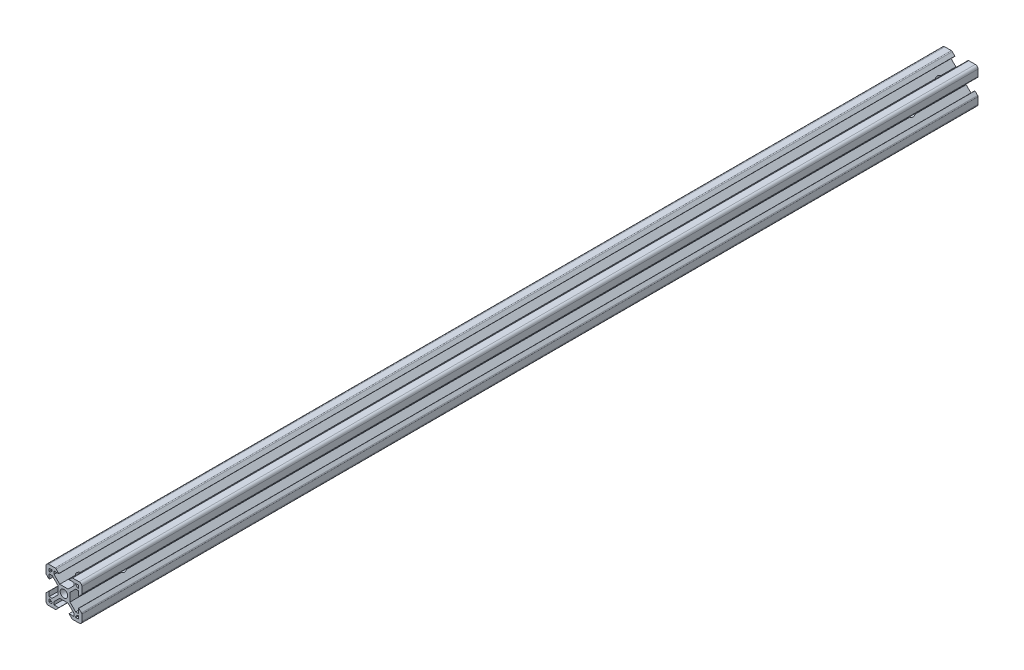
SolidWorks part; units mm, degrees
ref_plane "Front Plane" through (0, 0, 0) normal (0, 0, 1) x (1, 0, 0)
ref_plane "Top Plane" through (0, 0, 0) normal (0, 1, 0) x (1, 0, 0)
ref_plane "Right Plane" through (0, 0, 0) normal (1, 0, 0) x (0, 0, -1)
sketch "Sketch2" plane through (0, 0, 0) normal (0, 0, 1) x (1, 0, 0)
  line L0 (-8.2, 2.89) -> (-8.2, 5.5)
  line L1 (-2.1, 0) -> (-10, 0) construction
  line L2 (0, 2.1) -> (0, 10) construction
  line L3 (-4.9072, 10) -> (-8.5, 10)
  line L4 (-10, 4.9072) -> (-10, 8.5)
  line L5 (-2.1, 0) -> (-3.4, 0) construction
  line L6 (0, 2.1) -> (0, 3.4) construction
  line L7 (0, 3.4) -> (-2.3393, 3.4)
  line L8 (-3.4, 0) -> (-3.4, 2.3393)
  line L9 (-2.89, 8.2) -> (-5.5, 8.2)
  line L10 (-6.57, 8.2) -> (-6.57, 7.66)
  line L11 (-8.2, 6.57) -> (-7.66, 6.57)
  line L12 (-5.5, 8.2) -> (-5.5, 6.5607)
  line L13 (-6.5607, 5.5) -> (-8.2, 5.5)
  line L14 (-8.2, 8.2) -> (-1.4849, 1.4849) construction
  line L15 (-6.5607, 5.5) -> (-3.4, 2.3393)
  line L16 (-5.5, 6.5607) -> (-2.3393, 3.4)
  line L17 (-7.66, 6.57) -> (-6.57, 7.66)
  line L18 (-8.7303, 7.6697) -> (-0.5303, -0.5303) construction
  line L19 (-7.6697, 8.7303) -> (0.5303, 0.5303) construction
  line L20 (-8.2, 8.2) -> (0, 0) construction
  line L21 (-8.2, 6.57) -> (-8.2, 8.2)
  line L22 (-8.2, 0) -> (-8.2, 8.2) construction
  line L23 (-6.57, 8.2) -> (-8.2, 8.2)
  line L24 (0, 8.2) -> (-8.2, 8.2) construction
  line L25 (-10, 0) -> (-10, 10) construction
  line L26 (0, 10) -> (-10, 10) construction
  line L27 (-2.89, 8.31) -> (-2.89, 8.2)
  line L29 (-8.31, 2.89) -> (-8.2, 2.89)
  line L30 (-4.3486, 9.7686) -> (-2.89, 8.31)
  line L31 (-8.31, 2.89) -> (-9.7686, 4.3486)
  arc A0 (0, 2.1) -> (-2.1, 0) centre (0, 0) ccw
  arc A1 (-10, 8.5) -> (-8.5, 10) centre (-8.5, 8.5) cw
  arc A2 (-9.7686, 4.3486) -> (-10, 4.9072) centre (-9.21, 4.9072) cw
  arc A3 (-4.3486, 9.7686) -> (-4.9072, 10) centre (-4.9072, 9.21) ccw
  point P29 (-10, 10)
  point P39 (-10, 4.58)
  point P42 (-4.58, 10)
  dimension "D3" = 2.1
  dimension "D15" = 1.5
  dimension "D22" = 0.79
  dimension "D1" = 10
  dimension "D2" = 10
  dimension "D4" = 1.8
  dimension "D5" = 3.43
  dimension "D6" = 3.43
  dimension "D7" = 0.54
  dimension "D8" = 0.54
  dimension "D9" = 1.07
  dimension "D10" = 1.07
  dimension "D11" = 3.4
  dimension "D12" = 3.4
  dimension "D16" = 7.11
  dimension "D17" = 0.11
  dimension "D18" = 1.69
  dimension "D19" = 0.11
  dimension "D20" = 7.11
  dimension "D21" = 1.69
  dimension "D13" = 0.75
  dimension "D14" = 0.75
sketch "Sketch6" plane through (0, 0, 0) normal (0, 0, 1) x (1, 0, 0)
  line L0 (-3.4, 0) -> (-3.4, 2.3393) construction
  line L1 (-6.5607, 5.5) -> (-3.4, 2.3393) construction
  line L2 (-6.5607, 5.5) -> (-8.2, 5.5) construction
  line L3 (-8.2, 2.89) -> (-8.2, 5.5) construction
  line L4 (-8.31, 2.89) -> (-8.2, 2.89) construction
  line L5 (-7.66, 6.57) -> (-6.57, 7.66)
  line L6 (-6.57, 7.66) -> (-6.57, 8.2)
  line L7 (-6.57, 8.2) -> (-8.2, 8.2)
  line L8 (-8.2, 8.2) -> (-8.2, 6.57)
  line L9 (-8.2, 6.57) -> (-7.66, 6.57)
  line L10 (-7.66, 6.57) -> (-6.57, 7.66)
  line L11 (-6.57, 7.66) -> (-6.57, 8.2)
  line L12 (-6.57, 8.2) -> (-8.2, 8.2)
  line L13 (-8.2, 8.2) -> (-8.2, 6.57)
  line L14 (-8.2, 6.57) -> (-7.66, 6.57)
  line L15 (-8.31, 2.89) -> (-9.7686, 4.3486) construction
  line L16 (-10, 4.9072) -> (-10, 8.5) construction
  line L17 (-4.9072, 10) -> (-8.5, 10) construction
  line L18 (-4.3486, 9.7686) -> (-2.89, 8.31) construction
  line L19 (-2.89, 8.31) -> (-2.89, 8.2) construction
  line L20 (-2.89, 8.2) -> (-5.5, 8.2) construction
  line L21 (-5.5, 8.2) -> (-5.5, 6.5607) construction
  line L22 (-5.5, 6.5607) -> (-2.3393, 3.4) construction
  line L23 (0, 3.4) -> (-2.3393, 3.4) construction
  line L24 (-3.4, -2.3393) -> (-3.4, 2.3393)
  line L25 (-6.5607, 5.5) -> (-3.4, 2.3393)
  line L26 (-6.5607, 5.5) -> (-8.2, 5.5)
  line L27 (-8.2, 2.89) -> (-8.2, 5.5)
  line L28 (-8.31, 2.89) -> (-8.2, 2.89)
  line L29 (-8.31, 2.89) -> (-9.7686, 4.3486)
  line L30 (-10, 4.9072) -> (-10, 8.5)
  line L31 (-4.9072, 10) -> (-8.5, 10)
  line L32 (-4.3486, 9.7686) -> (-2.89, 8.31)
  line L33 (-2.89, 8.31) -> (-2.89, 8.2)
  line L34 (-2.89, 8.2) -> (-5.5, 8.2)
  line L35 (-5.5, 8.2) -> (-5.5, 6.5607)
  line L36 (-5.5, 6.5607) -> (-2.3393, 3.4)
  line L37 (2.3393, 3.4) -> (-2.3393, 3.4)
  line L38 (0, 2.1) -> (0, 10) construction
  line L39 (-2.1, 0) -> (-10, 0) construction
  line L40 (0, 2.1) -> (0, 10) construction
  line L41 (-2.1, 0) -> (-10, 0) construction
  line L42 (2.1, 0) -> (10, 0) construction
  line L43 (5.5, 6.5607) -> (2.3393, 3.4)
  line L44 (5.5, 8.2) -> (5.5, 6.5607)
  line L45 (2.89, 8.2) -> (5.5, 8.2)
  line L46 (2.89, 8.31) -> (2.89, 8.2)
  line L47 (4.3486, 9.7686) -> (2.89, 8.31)
  line L48 (4.9072, 10) -> (8.5, 10)
  line L49 (10, 4.9072) -> (10, 8.5)
  line L50 (8.31, 2.89) -> (9.7686, 4.3486)
  line L51 (8.31, 2.89) -> (8.2, 2.89)
  line L52 (8.2, 2.89) -> (8.2, 5.5)
  line L53 (6.5607, 5.5) -> (8.2, 5.5)
  line L54 (6.5607, 5.5) -> (3.4, 2.3393)
  line L55 (3.4, -2.3393) -> (3.4, 2.3393)
  line L56 (8.2, 6.57) -> (7.66, 6.57)
  line L57 (8.2, 8.2) -> (8.2, 6.57)
  line L58 (6.57, 8.2) -> (8.2, 8.2)
  line L59 (6.57, 7.66) -> (6.57, 8.2)
  line L60 (7.66, 6.57) -> (6.57, 7.66)
  line L61 (0, -2.1) -> (0, -10) construction
  line L62 (7.66, -6.57) -> (6.57, -7.66)
  line L63 (6.57, -7.66) -> (6.57, -8.2)
  line L64 (6.57, -8.2) -> (8.2, -8.2)
  line L65 (8.2, -8.2) -> (8.2, -6.57)
  line L66 (8.2, -6.57) -> (7.66, -6.57)
  line L67 (6.5607, -5.5) -> (3.4, -2.3393)
  line L68 (6.5607, -5.5) -> (8.2, -5.5)
  line L69 (8.2, -2.89) -> (8.2, -5.5)
  line L70 (8.31, -2.89) -> (8.2, -2.89)
  line L71 (8.31, -2.89) -> (9.7686, -4.3486)
  line L72 (10, -4.9072) -> (10, -8.5)
  line L73 (4.9072, -10) -> (8.5, -10)
  line L74 (4.3486, -9.7686) -> (2.89, -8.31)
  line L75 (2.89, -8.31) -> (2.89, -8.2)
  line L76 (2.89, -8.2) -> (5.5, -8.2)
  line L77 (5.5, -8.2) -> (5.5, -6.5607)
  line L78 (5.5, -6.5607) -> (2.3393, -3.4)
  line L79 (2.3393, -3.4) -> (-2.3393, -3.4)
  line L80 (-5.5, -6.5607) -> (-2.3393, -3.4)
  line L81 (-5.5, -8.2) -> (-5.5, -6.5607)
  line L82 (-2.89, -8.2) -> (-5.5, -8.2)
  line L83 (-2.89, -8.31) -> (-2.89, -8.2)
  line L84 (-4.3486, -9.7686) -> (-2.89, -8.31)
  line L85 (-4.9072, -10) -> (-8.5, -10)
  line L86 (-10, -4.9072) -> (-10, -8.5)
  line L87 (-8.31, -2.89) -> (-9.7686, -4.3486)
  line L88 (-8.31, -2.89) -> (-8.2, -2.89)
  line L89 (-8.2, -2.89) -> (-8.2, -5.5)
  line L90 (-6.5607, -5.5) -> (-8.2, -5.5)
  line L91 (-6.5607, -5.5) -> (-3.4, -2.3393)
  line L92 (-8.2, -6.57) -> (-7.66, -6.57)
  line L93 (-8.2, -8.2) -> (-8.2, -6.57)
  line L94 (-6.57, -8.2) -> (-8.2, -8.2)
  line L95 (-6.57, -7.66) -> (-6.57, -8.2)
  line L96 (-7.66, -6.57) -> (-6.57, -7.66)
  arc A0 (0, 2.1) -> (-2.1, 0) centre (0, 0) ccw construction
  arc A1 (-10, 4.9072) -> (-9.7686, 4.3486) centre (-9.21, 4.9072) ccw construction
  arc A2 (-8.5, 10) -> (-10, 8.5) centre (-8.5, 8.5) ccw construction
  arc A3 (-4.3486, 9.7686) -> (-4.9072, 10) centre (-4.9072, 9.21) ccw construction
  circle A4 centre (0, 0) radius 2.1
  arc A5 (-10, 4.9072) -> (-9.7686, 4.3486) centre (-9.21, 4.9072) ccw
  arc A6 (-8.5, 10) -> (-10, 8.5) centre (-8.5, 8.5) ccw
  arc A7 (-4.3486, 9.7686) -> (-4.9072, 10) centre (-4.9072, 9.21) ccw
  arc A8 (4.3486, 9.7686) -> (4.9072, 10) centre (4.9072, 9.21) cw
  arc A9 (8.5, 10) -> (10, 8.5) centre (8.5, 8.5) cw
  arc A10 (10, 4.9072) -> (9.7686, 4.3486) centre (9.21, 4.9072) cw
  arc A11 (10, -4.9072) -> (9.7686, -4.3486) centre (9.21, -4.9072) ccw
  arc A12 (8.5, -10) -> (10, -8.5) centre (8.5, -8.5) ccw
  arc A13 (4.3486, -9.7686) -> (4.9072, -10) centre (4.9072, -9.21) ccw
  arc A14 (-4.3486, -9.7686) -> (-4.9072, -10) centre (-4.9072, -9.21) cw
  arc A15 (-8.5, -10) -> (-10, -8.5) centre (-8.5, -8.5) cw
  arc A16 (-10, -4.9072) -> (-9.7686, -4.3486) centre (-9.21, -4.9072) cw
  point P85 (3.4, 0)
  dimension "D1" = 0
extrude "Boss-Extrude1" add sketch "Sketch6" against normal blind 500
sketch "Sketch7" plane through (0, 0, 0) normal (0, 1, 0) x (1, 0, 0)
  line L0 (2.3393, 500) -> (-2.3393, 500) construction
  line L1 (0, -11) -> (0, 11) construction
  circle A0 centre (0, 490) radius 2.75
  dimension "D1" = 10
  dimension "D2" = 5.5
extrude "Cut-Extrude1" cut sketch "Sketch7" against normal through all and the other way through all
sketch "Sketch8" plane through (0, 0, 0) normal (1, 0, 0) x (0, 0, -1)
  line L0 (11, 0) -> (-11, 0) construction
  line L1 (500, -2.3393) -> (500, 2.3393) construction
  circle A0 centre (470, 0) radius 2.75
  dimension "D2" = 5.5
  dimension "D1" = 30
extrude "Cut-Extrude2" cut sketch "Sketch8" against normal through all and the other way through all
ref_plane "Middle" through (0, 0, -250) normal (0, 0, 1) x (1, 0, 0)
mirror "Mirror1" about plane through (0, 0, -250) normal (0, 0, 1) of "Cut-Extrude1", "Cut-Extrude2"
